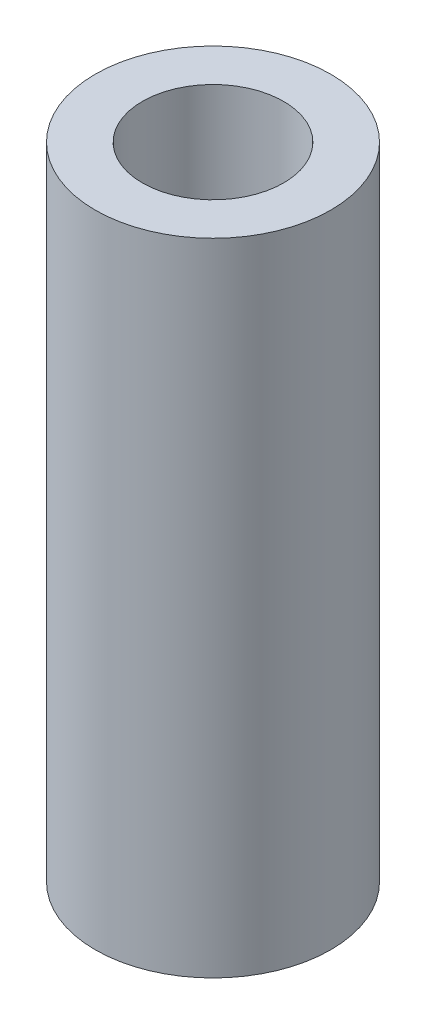
SolidWorks part; units mm, degrees
ref_plane "Front Plane" through (0, 0, 0) normal (0, 0, 1) x (1, 0, 0)
ref_plane "Top Plane" through (0, 0, 0) normal (0, 1, 0) x (1, 0, 0)
ref_plane "Right Plane" through (0, 0, 0) normal (1, 0, 0) x (0, 0, -1)
sketch "Sketch1" plane through (0, 0, 0) normal (0, 1, 0) x (1, 0, 0)
  circle A0 centre (0, 0) radius 3.81
  circle A1 centre (0, 0) radius 6.35
  dimension "D1" = 7.62
  dimension "D3" = 12.7
extrude "Boss-Extrude1" add sketch "Sketch1" along normal blind 34.544
